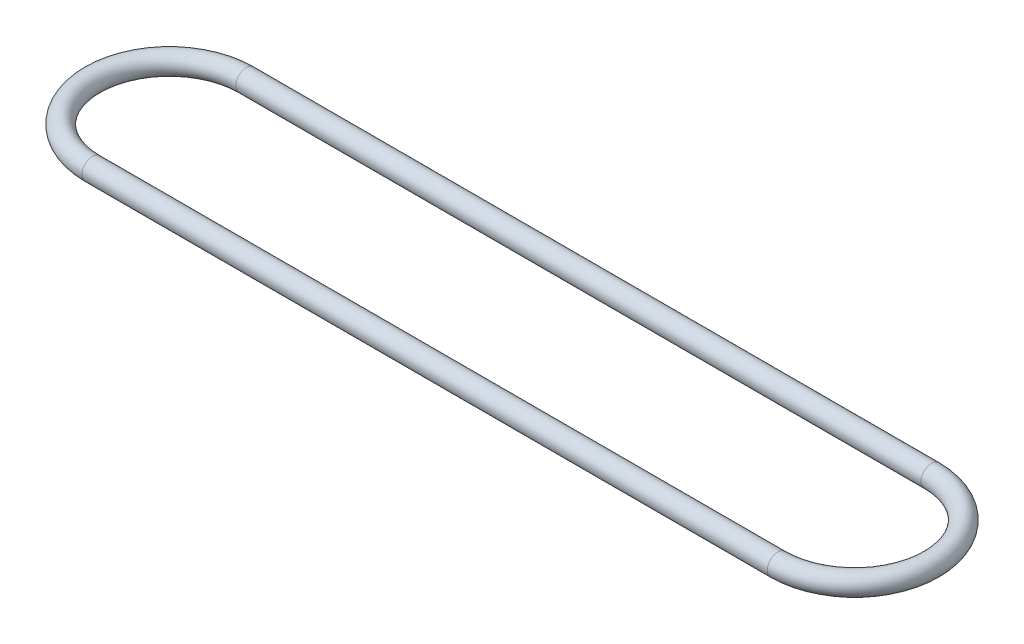
SolidWorks part; units mm, degrees
ref_plane "Front Plane" through (0, 0, 0) normal (0, 0, 1) x (1, 0, 0)
ref_plane "Top Plane" through (0, 0, 0) normal (0, 1, 0) x (1, 0, 0)
ref_plane "Right Plane" through (0, 0, 0) normal (1, 0, 0) x (0, 0, -1)
sketch "Croquis1" plane through (0, 0, 0) normal (0, 1, 0) x (1, 0, 0)
  line L0 (0, 0) -> (228, 0) construction
  line L1 (0, 25.58) -> (228, 25.58)
  line L2 (0, -25.58) -> (228, -25.58)
  arc A2 (0, 25.58) -> (0, -25.58) centre (0, 0) ccw
  arc A4 (0, 25.58) -> (0, -25.58) centre (0, 0) ccw
  arc A5 (228, -25.58) -> (228, 25.58) centre (228, 0) ccw
  point P1 (114, 0)
  point P11 (0, 25.58)
  dimension "D1" = 228
  dimension "D3" = 51.16
sketch "Croquis5" plane through (0, 0, 0) normal (1, 0, 0) x (0, 0, -1)
  circle A0 centre (25.58, 0) radius 3.5
  point P2 (0, 0)
  point P3 (0, 0)
  point P4 (0, 0)
  point P6 (26.1565, 0)
  point P7 (0, 0)
  point P8 (0, 0)
  dimension "D1" = 7
sweep "Barrer1" add profiles "Croquis5" path "Croquis1"
